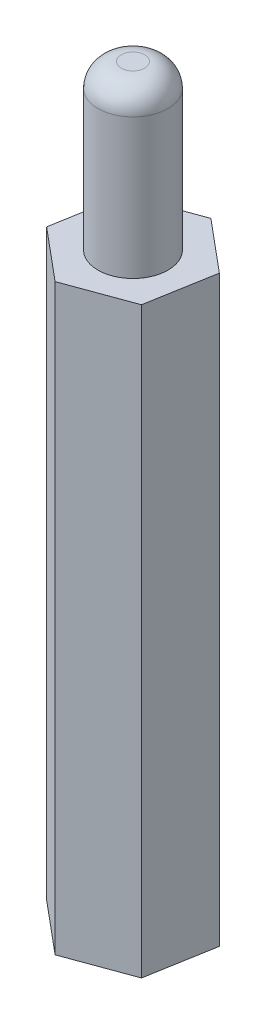
SolidWorks part; units mm, degrees
ref_plane "Front Plane" through (0, 0, 0) normal (0, 0, 1) x (1, 0, 0)
ref_plane "Top Plane" through (0, 0, 0) normal (0, 1, 0) x (1, 0, 0)
ref_plane "Right Plane" through (0, 0, 0) normal (1, 0, 0) x (0, 0, -1)
sketch "Sketch1" plane through (0, 0, 0) normal (0, 1, 0) x (1, 0, 0)
  line L1 (2.2148, -1.8515) -> (2.7108, 0.9924)
  line L2 (2.7108, 0.9924) -> (0.496, 2.8438)
  line L3 (0.496, 2.8438) -> (-2.2148, 1.8515)
  line L4 (-2.2148, 1.8515) -> (-2.7108, -0.9924)
  line L5 (-2.7108, -0.9924) -> (-0.496, -2.8438)
  line L6 (-0.496, -2.8438) -> (2.2148, -1.8515)
  circle A0 centre (0, 0) radius 2.5 construction
  dimension "D1" = 5
extrude "Boss-Extrude1" add sketch "Sketch1" along normal blind 25
sketch "Sketch2" plane through (0, 25, 0) normal (0, 1, 0) x (1, 0, 0)
  circle A0 centre (0, 0) radius 1.5
  dimension "D1" = 3
extrude "Boss-Extrude2" add sketch "Sketch2" along normal blind 7
sketch "Sketch3" plane through (0, 0, 0) normal (0, -1, 0) x (1, 0, 0)
  circle A0 centre (0, 0) radius 1.5
extrude "Cut-Extrude1" cut sketch "Sketch3" against normal blind 7
fillet "Fillet1" radius 1 1 edges at (0, 32, 1.5)
